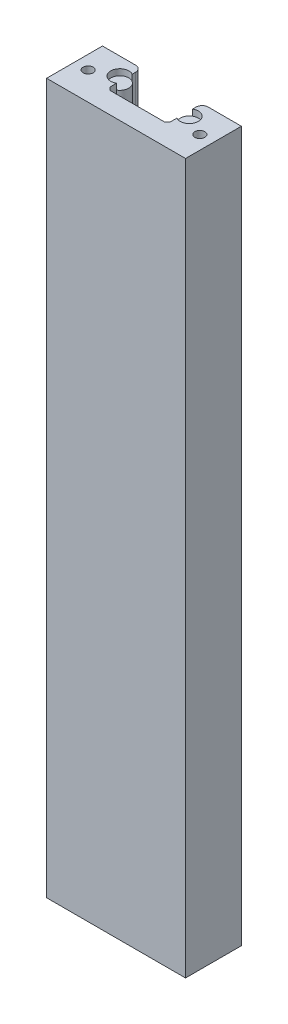
SolidWorks part; units mm, degrees
ref_plane "Front Plane" through (0, 0, 0) normal (0, 0, 1) x (1, 0, 0)
ref_plane "Top Plane" through (0, 0, 0) normal (0, 1, 0) x (1, 0, 0)
ref_plane "Right Plane" through (0, 0, 0) normal (1, 0, 0) x (0, 0, -1)
sketch "Sketch1" plane through (0, 0, 0) normal (0, 1, 0) x (1, 0, 0)
  line L0 (23, 0) -> (-23, 0)
  line L1 (-23, 0) -> (-23, 18.5)
  line L2 (-23, 18.5) -> (-10, 18.5)
  line L3 (-10, 18.5) -> (-10, 15.3481)
  line L4 (-10, 7) -> (10, 7)
  line L6 (0, 7) -> (0, 0) construction
  line L7 (-10, 10.1519) -> (-10, 7)
  line L8 (10, 10.1519) -> (10, 7)
  line L9 (10, 18.5) -> (10, 15.3481)
  line L10 (23, 18.5) -> (10, 18.5)
  line L11 (23, 0) -> (23, 18.5)
  arc A0 (-10, 15.3481) -> (-10, 10.1519) centre (-11.5, 12.75) ccw
  arc A1 (10, 15.3481) -> (10, 10.1519) centre (11.5, 12.75) cw
  dimension "D5" = 6
  dimension "D1" = 23
  dimension "D2" = 18.5
  dimension "D3" = 13
  dimension "D4" = 7
  dimension "D6" = 1.5
  dimension "D7" = 5.75
extrude "Boss-Extrude1" add sketch "Sketch1" along normal mid plane 235
sketch "Sketch2" plane through (0, 0, 0) normal (0, 1, 0) x (1, 0, 0)
  line L0 (0, 0) -> (0, 7) construction
  line L1 (10, 7) -> (-10, 7) construction
  circle A0 centre (-11.5, 12.75) radius 2.95
  circle A1 centre (11.5, 12.75) radius 2.95
  dimension "D1" = 5.9
extrude "Boss-Extrude2" add sketch "Sketch2" along normal mid plane 231 separate body
chamfer "Chamfer1" distance 1 angle 45 2 edges at (10, 0, -7) (-10, 0, -7)
fillet "Fillet1" radius 2 2 edges at (10, 0, -18.5) (-10, 0, -18.5)
sketch "Sketch3" plane through (0, 117.5, 0) normal (0, 1, 0) x (1, 0, 0)
  line L0 (-23, 9.25) -> (23, 9.25) construction
  line L1 (-23, 18.5) -> (-23, 0) construction
  line L2 (23, 0) -> (23, 18.5) construction
  line L3 (0, 0) -> (0, 7) construction
  line L4 (-23, 0) -> (23, 0) construction
  line L5 (9, 7) -> (-9, 7) construction
  circle A0 centre (-18.5, 9.25) radius 1.65
  circle A1 centre (18.5, 9.25) radius 1.65
  dimension "D1" = 18.5
  dimension "D2" = 3.3
extrude "Cut-Extrude1" cut sketch "Sketch3" against normal blind 25
sketch "Sketch4" plane through (0, -117.5, 0) normal (0, -1, 0) x (1, 0, 0)
  line L0 (0, 0) -> (0, -7) construction
  line L1 (9, -7) -> (-9, -7) construction
  line L2 (-23, -9.25) -> (23, -9.25) construction
  line L3 (-23, -18.5) -> (-23, 0) construction
  line L4 (23, 0) -> (23, -18.5) construction
  line L5 (-18.5, -9.25) -> (-18.5, -18.5) construction
  line L6 (-12, -18.5) -> (-23, -18.5) construction
  circle A0 centre (-18.5, -14.25) radius 1.65
  circle A1 centre (-18.5, -4.25) radius 1.65
  circle A2 centre (18.5, -14.25) radius 1.65
  circle A3 centre (18.5, -4.25) radius 1.65
  point P17 (0, 0)
  point P18 (-18.5, -15.1669)
  dimension "D2" = 3.3
  dimension "D3" = 5
  dimension "D1" = 18.5
extrude "Cut-Extrude2" cut sketch "Sketch4" against normal blind 25
